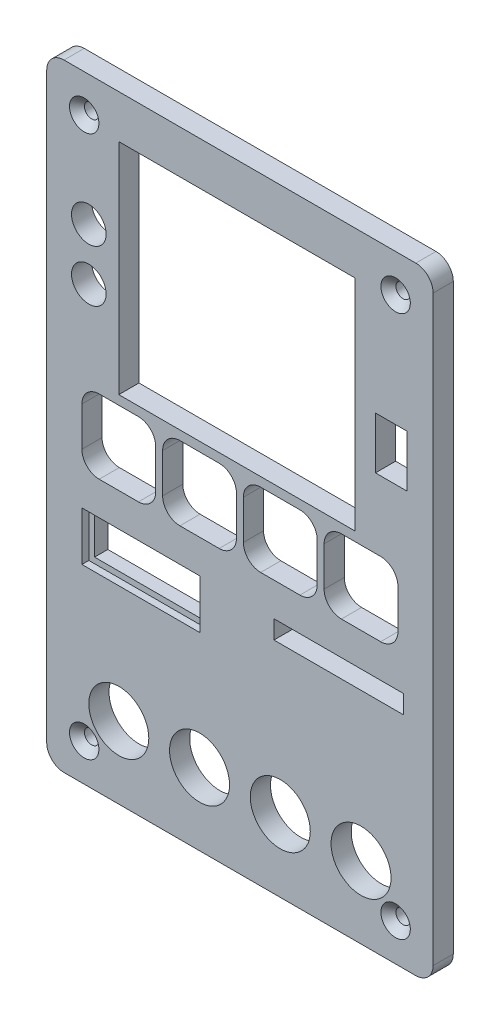
SolidWorks part; units mm, degrees
ref_plane "Přední rovina" through (0, 0, 0) normal (0, 0, 1) x (1, 0, 0)
ref_plane "Horní rovina" through (0, 0, 0) normal (0, 1, 0) x (1, 0, 0)
ref_plane "Pravá rovina" through (0, 0, 0) normal (1, 0, 0) x (0, 0, -1)
sketch "Skica1" plane through (0, 0, 0) normal (0, 0, 1) x (1, 0, 0)
  line L1 (0, 0) -> (67, 0)
  line L2 (0, 0) -> (0, 107)
  line L3 (0, 107) -> (67, 107)
  line L4 (67, 0) -> (67, 107)
  dimension "D1" = 67
  dimension "D2" = 107
extrude "Přidat vysunutím1" add sketch "Skica1" along normal blind 3.5
fillet "Zaoblit1" radius 3 4 edges at (67, 0, 1.75) (0, 0, 1.75) (0, 107, 1.75) (67, 107, 1.75)
sketch "Skica2" plane through (0, 0, 3.5) normal (0, 0, 1) x (1, 0, 0)
  line L0 (6.5, 100.5) -> (60.5, 100.5) construction
  line L1 (6.5, 100.5) -> (6.5, 6.5) construction
  line L2 (33.5, 107) -> (33.5, 100.5) construction
  line L3 (64, 107) -> (3, 107) construction
  line L4 (0, 53.5) -> (6.5, 53.5) construction
  line L5 (0, 104) -> (0, 3) construction
  line L6 (26.5, 12.5) -> (40.5, 12.5) construction
  line L7 (12.5, 99.5) -> (53.5, 99.5)
  line L8 (12.5, 99.5) -> (12.5, 61.5)
  line L9 (12.5, 61.5) -> (53.5, 61.5)
  line L10 (53.5, 99.5) -> (53.5, 61.5)
  line L11 (57, 81) -> (62.5, 81)
  line L12 (57, 81) -> (57, 72)
  line L13 (57, 72) -> (62.5, 72)
  line L14 (62.5, 81) -> (62.5, 72)
  line L15 (48.1, 59.9) -> (60.9, 59.9)
  line L16 (48.1, 59.9) -> (48.1, 47.1)
  line L17 (48.1, 47.1) -> (60.9, 47.1)
  line L18 (60.9, 59.9) -> (60.9, 47.1)
  line L19 (34.1, 59.9) -> (46.9, 59.9)
  line L20 (34.1, 59.9) -> (34.1, 47.1)
  line L21 (34.1, 47.1) -> (46.9, 47.1)
  line L22 (46.9, 59.9) -> (46.9, 47.1)
  line L23 (20.1, 59.9) -> (32.9, 59.9)
  line L24 (20.1, 59.9) -> (20.1, 47.1)
  line L25 (20.1, 47.1) -> (32.9, 47.1)
  line L26 (32.9, 59.9) -> (32.9, 47.1)
  line L27 (6.1, 59.9) -> (18.9, 59.9)
  line L28 (6.1, 59.9) -> (6.1, 47.1)
  line L29 (6.1, 47.1) -> (18.9, 47.1)
  line L30 (18.9, 59.9) -> (18.9, 47.1)
  line L31 (39.4, 41.3) -> (61.9, 41.3)
  line L32 (39.4, 41.3) -> (39.4, 38.1)
  line L33 (39.4, 38.1) -> (61.9, 38.1)
  line L34 (61.9, 41.3) -> (61.9, 38.1)
  line L35 (33.5, 12.5) -> (33.5, 0) construction
  line L36 (3, 0) -> (64, 0) construction
  line L37 (33.5, 100.5) -> (33.5, 99.5) construction
  line L38 (67, 3) -> (67, 104) construction
  circle A0 centre (6.5, 100.5) radius 1.25
  circle A1 centre (60.5, 100.5) radius 1.25
  circle A2 centre (6.5, 6.5) radius 1.25
  circle A3 centre (60.5, 6.5) radius 1.25
  circle A4 centre (7.3, 75.5) radius 3
  circle A5 centre (12.5, 12.5) radius 5.2
  circle A6 centre (26.5, 12.5) radius 5.2
  circle A7 centre (40.5, 12.5) radius 5.2
  circle A8 centre (54.5, 12.5) radius 5.2
  circle A9 centre (7.3, 84.5) radius 3
  point P58 (12.5, 59.9)
  point P59 (26.5, 59.9)
  point P62 (40.5, 59.9)
  point P63 (54.5, 59.9)
  point P64 (6.1, 53.5)
  point P65 (0, 0)
  point P69 (0, 0)
  dimension "D1" = 2.5
  dimension "D2" = 2.5
  dimension "D3" = 2.5
  dimension "D4" = 2.5
  dimension "D7" = 10.4
  dimension "D8" = 10.4
  dimension "D9" = 10.4
  dimension "D10" = 10.4
  dimension "D15" = 12.8
  dimension "D36" = 6
  dimension "D37" = 6
  dimension "D5" = 54
  dimension "D6" = 94
  dimension "D11" = 14
  dimension "D12" = 14
  dimension "D13" = 14
  dimension "D14" = 12.5
  dimension "D16" = 12.8
  dimension "D17" = 12.8
  dimension "D18" = 12.8
  dimension "D19" = 12.8
  dimension "D20" = 14
  dimension "D21" = 14
  dimension "D22" = 14
  dimension "D23" = 12.5
  dimension "D24" = 53.5
  dimension "D25" = 41
  dimension "D26" = 38
  dimension "D27" = 7.5
  dimension "D28" = 3.2
  dimension "D29" = 22.5
  dimension "D30" = 5.1
  dimension "D31" = 41.3
  dimension "D32" = 5.5
  dimension "D33" = 9
  dimension "D34" = 3.5
  dimension "D35" = 10.5
  dimension "D38" = 22.5
  dimension "D39" = 7.3
  dimension "D40" = 31.5
  dimension "D41" = 7.3
  dimension "D42" = 4.5
extrude "Odebrat vysunutím1" cut sketch "Skica2" against normal through all
fillet "Zaoblit2" radius 3 16 edges at (18.9, 59.9, 1.75) (32.9, 59.9, 1.75) (46.9, 59.9, 1.75) (46.9, 47.1, 1.75) (32.9, 47.1, 1.75) (18.9, 47.1, 1.75) (6.1, 47.1, 1.75) (20.1, 47.1, 1.75) (34.1, 47.1, 1.75) (6.1, 59.9, 1.75) (20.1, 59.9, 1.75) (34.1, 59.9, 1.75) (48.1, 59.9, 1.75) (48.1, 47.1, 1.75) (60.9, 47.1, 1.75) (60.9, 59.9, 1.75)
sketch "Skica3" plane through (0, 0, 0) normal (0, 0, -1) x (-1, 0, 0)
  line L0 (-53.5, 99.5) -> (-12.5, 99.5) construction
  line L1 (-22, 99.5) -> (-44, 99.5)
  line L2 (-22, 99.5) -> (-22, 102.5)
  line L3 (-22, 102.5) -> (-44, 102.5)
  line L4 (-44, 99.5) -> (-44, 102.5)
  line L5 (-33, 99.5) -> (-33, 102.5) construction
  dimension "D1" = 22
  dimension "D2" = 3
extrude "Odebrat vysunutím2" cut sketch "Skica3" against normal blind 2
chamfer "Zkosení1" distance 1.3 angle 45 4 edges at (61.75, 6.5, 3.5) (7.75, 6.5, 3.5) (61.75, 100.5, 3.5) (7.75, 100.5, 3.5)
sketch "Skica4" plane through (0, 0, 3.5) normal (0, 0, 1) x (1, 0, 0)
  line L0 (61.9, 41.3) -> (39.4, 41.3) construction
  line L1 (26.6, 32.8) -> (6.1, 32.8)
  line L2 (26.6, 32.8) -> (26.6, 41.3)
  line L3 (26.6, 41.3) -> (6.1, 41.3)
  line L4 (6.1, 32.8) -> (6.1, 41.3)
  line L5 (6.1, 56.9) -> (6.1, 50.1) construction
  dimension "D1" = 20.5
  dimension "D2" = 8.5
extrude "Odebrat vysunutím3" cut sketch "Skica4" against normal blind 1.2
sketch "Skica5" plane through (0, 0, 2.3) normal (0, 0, 1) x (1, 0, 0)
  line L0 (26.6, 41.3) -> (6.1, 41.3) construction
  line L1 (7.1, 40.3) -> (25.6, 40.3)
  line L2 (7.1, 40.3) -> (7.1, 33.8)
  line L3 (7.1, 33.8) -> (25.6, 33.8)
  line L4 (25.6, 40.3) -> (25.6, 33.8)
  line L5 (26.6, 32.8) -> (26.6, 41.3) construction
  line L6 (6.1, 41.3) -> (6.1, 32.8) construction
  line L7 (6.1, 32.8) -> (26.6, 32.8) construction
  dimension "D1" = 1
  dimension "D2" = 1
  dimension "D3" = 1
  dimension "D4" = 1
extrude "Odebrat vysunutím4" cut sketch "Skica5" against normal through all
